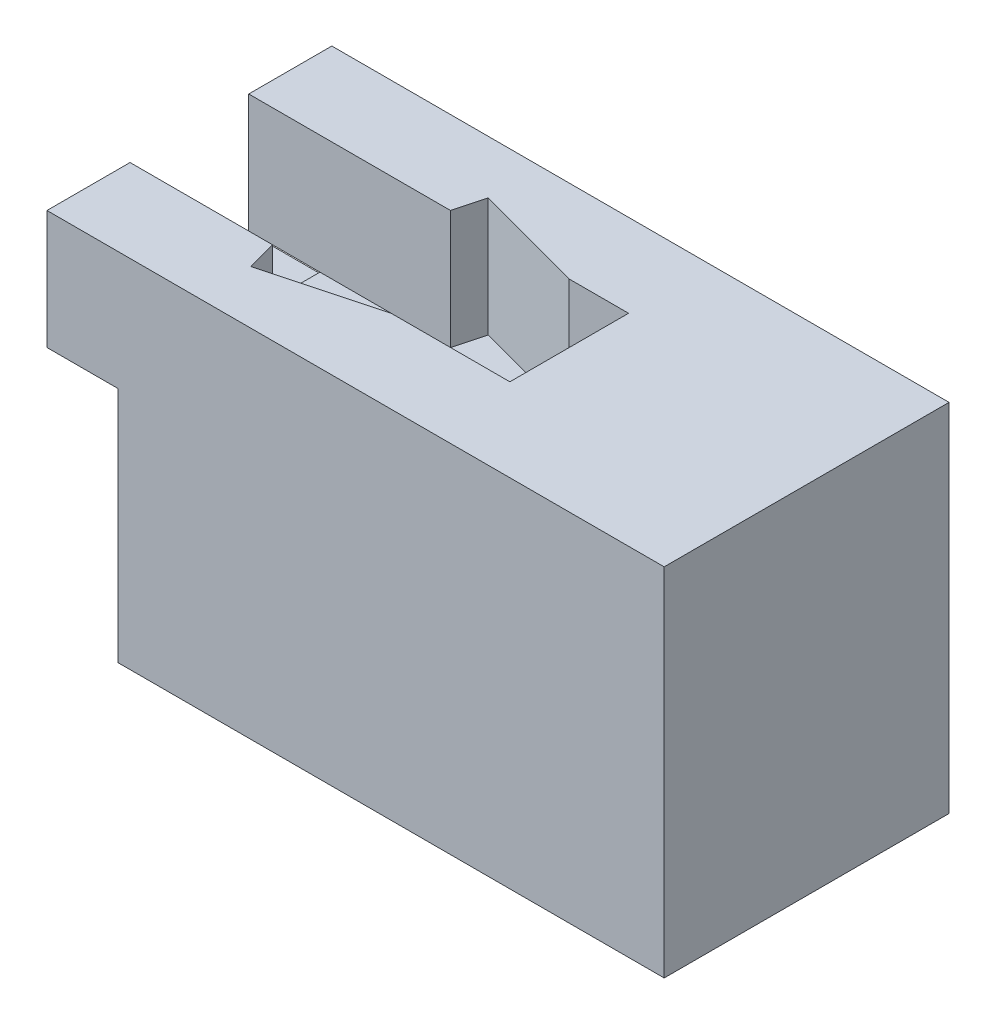
SolidWorks part; units mm, degrees
material "松木"
ref_plane "前视基准面" through (0, 0, 0) normal (0, 0, 1) x (1, 0, 0)
ref_plane "上视基准面" through (0, 0, 0) normal (0, 1, 0) x (1, 0, 0)
ref_plane "右视基准面" through (0, 0, 0) normal (1, 0, 0) x (0, 0, -1)
sketch "草图1" plane through (0, 0, 0) normal (1, 0, 0) x (0, 0, -1)
  line L5 (0, 0) -> (120, 0)
  line L6 (0, 0) -> (0, 150)
  line L7 (0, 150) -> (120, 150)
  line L8 (120, 0) -> (120, 150)
  dimension "D1" = 120
  dimension "D2" = 150
extrude "凸台-拉伸1" add sketch "草图1" along normal blind 200
sketch "草图2" plane through (0, 150, 0) normal (0, 1, 0) x (1, 0, 0)
  line L0 (0, 120) -> (0, 0) construction
  line L1 (0, 85) -> (100, 85)
  line L2 (0, 85) -> (0, 35)
  line L3 (0, 35) -> (100, 35)
  line L4 (100, 85) -> (100, 35)
  line L5 (200, 120) -> (200, 0) construction
  line L6 (50, 35) -> (46.6506, 47.5)
  line L7 (46.6506, 47.5) -> (0, 35)
  line L8 (75, 85) -> (71.6506, 72.5)
  line L9 (71.6506, 72.5) -> (25, 85)
  line L10 (75, 85) -> (28.3494, 97.5)
  line L11 (28.3494, 97.5) -> (25, 85)
  line L12 (0, 35) -> (3.3494, 22.5)
  line L13 (3.3494, 22.5) -> (50, 35)
  point P8 (200, 60)
  point P9 (100, 60)
  line M9 (0, 120) -> (0, 0)
  dimension "D1" = 50
  dimension "D2" = 100
  dimension "D3" = 50
  dimension "D4" = 75
  dimension "D5" = 15
  dimension "D6" = 25
  dimension "D7" = 50
  dimension "D8" = 75
  dimension "D9" = 15
extrude "切除-拉伸1" cut sketch "草图2" against normal blind 50 contours L9 L8 L1 | L10 L11 L1 | L8 L9 L1 L7 L6 L3 L4 M9 | L6 L7 L3 | L12 L13 L3
sketch "草图3" plane through (0, 0, 0) normal (-1, 0, 0) x (0, 0, 1)
  line L22 (-35, 100) -> (-85, 100)
  line L23 (-85, 100) -> (-85, 150)
  line L24 (-85, 150) -> (-120, 150)
  line L25 (-120, 150) -> (-120, 0)
  line L26 (-120, 0) -> (0, 0)
  line L27 (0, 0) -> (0, 150)
  line L28 (0, 150) -> (-35, 150)
  line L29 (-35, 150) -> (-35, 100)
  line L30 (-35, 100) -> (-85, 100)
  line L31 (-85, 100) -> (-85, 150)
  line L32 (-85, 150) -> (-120, 150)
  line L33 (-120, 150) -> (-120, 0)
  line L34 (-120, 0) -> (0, 0)
  line L35 (0, 0) -> (0, 150)
  line L36 (0, 150) -> (-35, 150)
  line L37 (-35, 150) -> (-35, 100)
  dimension "D1" = 0
extrude "凸台-拉伸3" add sketch "草图3" along normal blind 30
sketch "草图4" plane through (-30, 0, 0) normal (-1, 0, 0) x (0, 0, 1)
  line L21 (0, 150) -> (-35, 150)
  line L22 (-35, 150) -> (-35, 100)
  line L23 (-35, 100) -> (-85, 100)
  line L24 (-85, 100) -> (-85, 150)
  line L25 (-85, 150) -> (-120, 150) construction
  line L26 (-85, 100) -> (-85, 150) construction
  line L27 (-85, 150) -> (-120, 150)
  line L28 (-120, 150) -> (-120, 100)
  line L29 (-120, 150) -> (-120, 0) construction
  line L30 (-120, 100) -> (0, 100)
  line L31 (0, 0) -> (0, 150) construction
  line L32 (0, 100) -> (0, 150)
  line M9 (-35, 150) -> (-35, 100)
  line M11 (-85, 100) -> (-85, 150)
  line M12 (-85, 150) -> (-120, 150)
  line M13 (-120, 150) -> (-120, 0)
  line M15 (0, 0) -> (0, 150)
  line M16 (0, 150) -> (-35, 150)
extrude "凸台-拉伸4" add sketch "草图4" along normal blind 30 contours L30 M13 M11 M12 | L30 M9 M15 M16
sketch "草图5" plane through (-30, 0, 0) normal (-1, 0, 0) x (0, 0, 1)
  line L5 (-120, 0) -> (0, 0) construction
  line L10 (-85, 100) -> (-35, 100)
  line L11 (-85, 100) -> (-85, 0)
  line L12 (-85, 0) -> (-35, 0)
  line L13 (-35, 100) -> (-35, 0)
  line L14 (-85, 99.5) -> (-35, 99.5)
  line M9 (-120, 0) -> (0, 0)
  dimension "D1" = 50
  dimension "D2" = 0.5
extrude "凸台-拉伸7" add sketch "草图5" along normal blind 30 contours L14 L11 L13 M9
